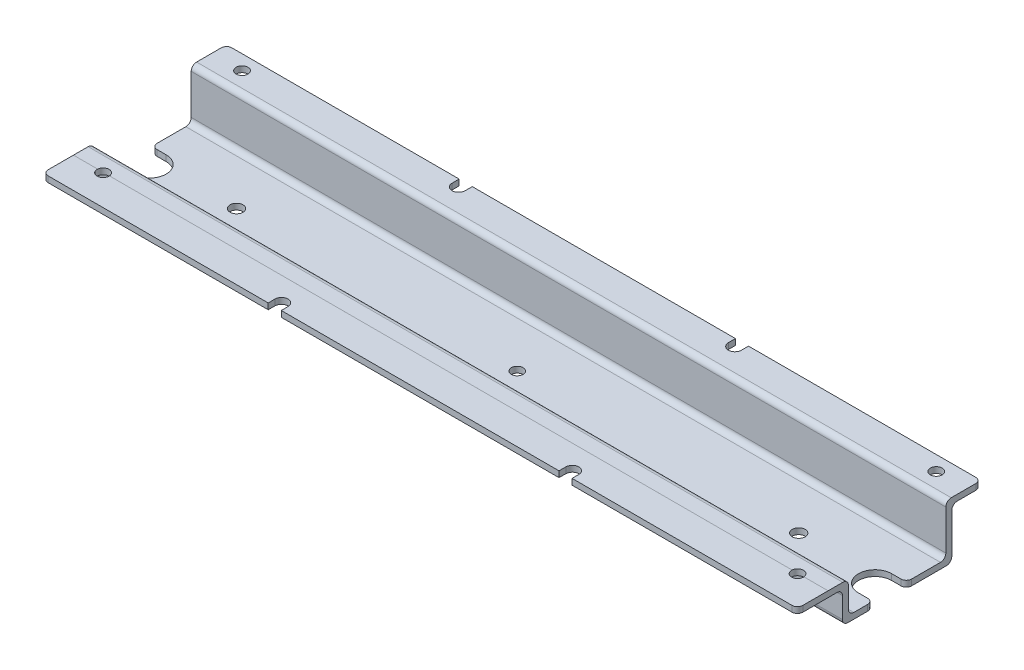
SolidWorks part; units mm, degrees
material "Plain Carbon Steel"
ref_plane "Front Plane" through (0, 0, 0) normal (0, 0, 1) x (1, 0, 0)
ref_plane "Top Plane" through (0, 0, 0) normal (0, 1, 0) x (1, 0, 0)
ref_plane "Right Plane" through (0, 0, 0) normal (1, 0, 0) x (0, 0, -1)
sketch "Sketch1" plane through (0, 0, 0) normal (1, 0, 0) x (0, 0, -1)
  line L0 (-15.04, 0) -> (15.04, 0)
  line L1 (55, 0) -> (-55, 0) construction
  line L2 (-13.6, 1.59) -> (13.6, 1.59)
  line L3 (-15.04, 8.6) -> (-15.04, 3.03)
  line L4 (15.04, 13.7) -> (15.04, 3.03)
  line L5 (16.48, 15.14) -> (24.5, 15.14)
  line L6 (-16.48, 10.04) -> (-24.68, 10.04)
  line L7 (24.5, 15.14) -> (24.5, 13.55)
  line L8 (24.5, 13.55) -> (18.07, 13.55)
  line L9 (16.63, 12.11) -> (16.63, 1.44)
  line L10 (15.19, 0) -> (15.04, 0)
  line L11 (-24.68, 10.04) -> (-24.68, 8.45)
  line L12 (-24.68, 8.45) -> (-18.07, 8.45)
  line L13 (-16.63, 7.01) -> (-16.63, 1.44)
  line L14 (-15.19, 0) -> (-15.04, 0)
  arc A0 (18.07, 13.55) -> (16.63, 12.11) centre (18.07, 12.11) ccw
  arc A1 (15.04, 13.7) -> (16.48, 15.14) centre (16.48, 13.7) cw
  arc A2 (16.63, 1.44) -> (15.19, 0) centre (15.19, 1.44) cw
  arc A3 (13.6, 1.59) -> (15.04, 3.03) centre (13.6, 3.03) ccw
  arc A4 (-16.63, 1.44) -> (-15.19, 0) centre (-15.19, 1.44) ccw
  arc A5 (-13.6, 1.59) -> (-15.04, 3.03) centre (-13.6, 3.03) cw
  arc A6 (-18.07, 8.45) -> (-16.63, 7.01) centre (-18.07, 7.01) cw
  arc A7 (-15.04, 8.6) -> (-16.48, 10.04) centre (-16.48, 8.6) ccw
  point P8 (0, 0)
  point P12 (0, 0.3286)
  point P23 (15.04, 15.14)
  point P26 (16.63, 0)
  point P31 (-16.63, 0)
  point P38 (-15.04, 10.04)
  dimension "D6" = 1.44
  dimension "D1" = 9.64
  dimension "D2" = 10.04
  dimension "D3" = 1.59
  dimension "D4" = 9.46
  dimension "D5" = 15.14
  dimension "D7" = 15.04
extrude "Boss-Extrude1" add sketch "Sketch1" against normal blind 202
fillet "Fillet1" radius 1.44 1 edges at (0, 9.245, 24.68)
fillet "Fillet2" radius 1.44 3 edges at (0, 14.345, -24.5) (-202, 9.245, 24.68) (-202, 14.345, -24.5)
sketch "Sketch2" plane through (0, 10.04, 0) normal (0, 1, 0) x (1, 0, 0)
  line L0 (-202, 0) -> (0, 0) construction
  line L1 (-202, 13.6) -> (-202, -13.6) construction
  line L2 (-101, 24.5) -> (-101, -24.68) construction
  line L3 (-200.56, 24.5) -> (-1.44, 24.5) construction
  line L4 (-200.56, -24.68) -> (-1.44, -24.68) construction
  line L5 (-202, -16.48) -> (-202, -23.24) construction
  line L6 (-202, 16.48) -> (0, 16.48) construction
  line L7 (0, 4.455) -> (0, -4.455)
  line L8 (-3.9, 4.455) -> (0, 4.455)
  line L9 (-141.6699, -24.68) -> (-141.6699, -22.87)
  line L10 (-138.1699, -24.68) -> (-141.6699, -24.68)
  line L11 (-138.1699, -22.87) -> (-138.1699, -24.68)
  line L12 (-63.8301, -22.87) -> (-63.8301, -24.68)
  line L13 (-63.8301, -24.68) -> (-60.3301, -24.68)
  line L14 (-60.3301, -24.68) -> (-60.3301, -22.87)
  line L15 (0, -4.455) -> (-3.9, -4.455)
  line L16 (-202, 23.06) -> (-202, 16.48) construction
  line L17 (-139.73, 24.5) -> (-136.23, 24.5)
  line L18 (-202, 4.455) -> (-202, -4.455)
  line L19 (-202, -4.455) -> (-198.1, -4.455)
  line L20 (-136.23, 24.5) -> (-136.23, 22.6)
  line L21 (-198.1, 4.455) -> (-202, 4.455)
  line L22 (-139.73, 24.5) -> (-139.73, 22.6)
  line L23 (-62.27, 24.5) -> (-62.27, 22.6)
  line L24 (-62.27, 24.5) -> (-65.77, 24.5)
  line L25 (-65.77, 24.5) -> (-65.77, 22.6)
  circle A0 centre (-193.95, -20.6) radius 1.59
  arc A1 (-138.1699, -22.87) -> (-141.6699, -22.87) centre (-139.9199, -22.87) ccw
  circle A2 centre (-8.05, -20.6) radius 1.59
  arc A3 (-63.8301, -22.87) -> (-60.3301, -22.87) centre (-62.0801, -22.87) cw
  circle A4 centre (-176.235, 1.415) radius 1.735
  arc A5 (-3.9, 4.455) -> (-3.9, -4.455) centre (-3.9, 0) ccw
  circle A6 centre (-25.765, 1.415) radius 1.735
  circle A7 centre (-193.91, 20.563) radius 1.59
  arc A8 (-198.1, 4.455) -> (-198.1, -4.455) centre (-198.1, 0) cw
  circle A9 centre (-101, 1.31) radius 1.57
  arc A10 (-139.73, 22.6) -> (-136.23, 22.6) centre (-137.98, 22.6) ccw
  arc A11 (-62.27, 22.6) -> (-65.77, 22.6) centre (-64.02, 22.6) cw
  circle A12 centre (-8.09, 20.563) radius 1.59
  point P47 (-202, 0)
  dimension "D3" = 3.18
  dimension "D4" = 1.75
  dimension "D8" = 4.455
  dimension "D12" = 3.47
  dimension "D14" = 25.765
  dimension "D17" = 8.09
  dimension "D15" = 3.18
  dimension "D18" = 1.75
  dimension "D1" = 4.08
  dimension "D2" = 8.05
  dimension "D5" = 1.81
  dimension "D6" = 1.81
  dimension "D7" = 3.5
  dimension "D9" = 3.9
  dimension "D10" = 3.9
  dimension "D11" = 8.91
  dimension "D13" = 15.065
  dimension "D16" = 3.937
  dimension "D19" = 1.9
  dimension "D20" = 1.9
  dimension "D21" = 3.5
  dimension "D22" = 62.27
  dimension "D23" = 23.19
extrude "Cut-Extrude1" cut sketch "Sketch2" against normal through all both and the other way through all
fillet "Fillet3" radius 1.44 4 edges at (0, 0.795, -4.455) (0, 0.795, 4.455) (-202, 0.795, -4.455) (-202, 0.795, 4.455)
sketch "Sketch3" plane through (-202, 0, 0) normal (-1, 0, 0) x (0, 0, 1)
  line L0 (15.04, 3.03) -> (15.04, 8.6) construction
  line L1 (15.04, 3.03) -> (15.04, 8.6)
  line L10 (5.895, 1.59) -> (13.6, 1.59) construction
  line L11 (11.04, 3.03) -> (11.04, 8.6)
  line L12 (16.48, 10.04) -> (23.24, 10.04) construction
  line L13 (12.5519, 10.0382) -> (16.48, 10.04)
  line L14 (9.6, 1.59) -> (13.6, 1.59)
  arc A0 (16.48, 10.04) -> (15.04, 8.6) centre (16.48, 8.6) ccw construction
  arc A1 (13.6, 1.59) -> (15.04, 3.03) centre (13.6, 3.03) ccw construction
  arc A2 (16.48, 10.04) -> (15.04, 8.6) centre (16.48, 8.6) ccw
  arc A3 (13.6, 1.59) -> (15.04, 3.03) centre (13.6, 3.03) ccw
  arc A8 (9.6, 1.59) -> (11.04, 3.03) centre (9.6, 3.03) ccw
  arc A9 (11.04, 8.6) -> (12.5519, 10.0382) centre (12.48, 8.6) cw
  dimension "D2" = 1.44
  dimension "D3" = 1.44
  dimension "D1" = 4
extrude "Boss-Extrude2" add sketch "Sketch3" against normal up to surface (202 mm away) up to face at (0, 5.02, 15.4125)
sketch "Sketch4" plane through (-202, 0, 0) normal (-1, 0, 0) x (0, 0, 1)
  line L0 (16.63, 7.01) -> (16.63, 1.44) construction
  line L1 (16.63, 7.01) -> (16.63, 1.44)
  line L2 (12.63, 7.01) -> (12.63, 1.44)
  line L3 (15.19, 0) -> (5.895, 0) construction
  line L4 (14.07, 8.45) -> (18.07, 8.45)
  line L5 (11.19, 0) -> (15.19, 0)
  arc A0 (15.19, 0) -> (16.63, 1.44) centre (15.19, 1.44) ccw construction
  arc A1 (18.07, 8.45) -> (16.63, 7.01) centre (18.07, 7.01) ccw construction
  arc A2 (15.19, 0) -> (16.63, 1.44) centre (15.19, 1.44) ccw
  arc A3 (18.07, 8.45) -> (16.63, 7.01) centre (18.07, 7.01) ccw
  arc A4 (14.07, 8.45) -> (12.63, 7.01) centre (14.07, 7.01) ccw
  arc A5 (12.63, 1.44) -> (11.19, 0) centre (11.19, 1.44) cw
  dimension "D2" = 1.44
  dimension "D3" = 1.44
  dimension "D1" = 4
extrude "Cut-Extrude2" cut sketch "Sketch4" against normal through all
sketch "Sketch5" plane through (0, 10.04, 0) normal (0, 1, 0) x (1, 0, 0)
  circle A0 centre (-193.95, -20.6) radius 1.59 construction
  circle A1 centre (-8.05, -20.6) radius 1.59 construction
  circle A2 centre (-193.95, -20.6) radius 1.59
  circle A3 centre (-8.05, -20.6) radius 1.59
  circle A4 centre (-193.95, -16.6) radius 1.59
  circle A5 centre (-8.05, -16.6) radius 1.59
  dimension "D1" = 3.18
  dimension "D4" = 3.18
  dimension "D2" = 4
  dimension "D3" = 4
extrude "Cut-Extrude3" cut sketch "Sketch5" against normal blind 10
sketch "Sketch6" plane through (0, 10.04, 0) normal (0, 1, 0) x (1, 0, 0)
  circle A0 centre (-193.95, -20.6) radius 1.59
  circle A1 centre (-8.05, -20.6) radius 1.59
extrude "Boss-Extrude3" add sketch "Sketch6" against normal up to surface (1.59 mm away) up to face at (-193.95, 8.45, 15.01)
